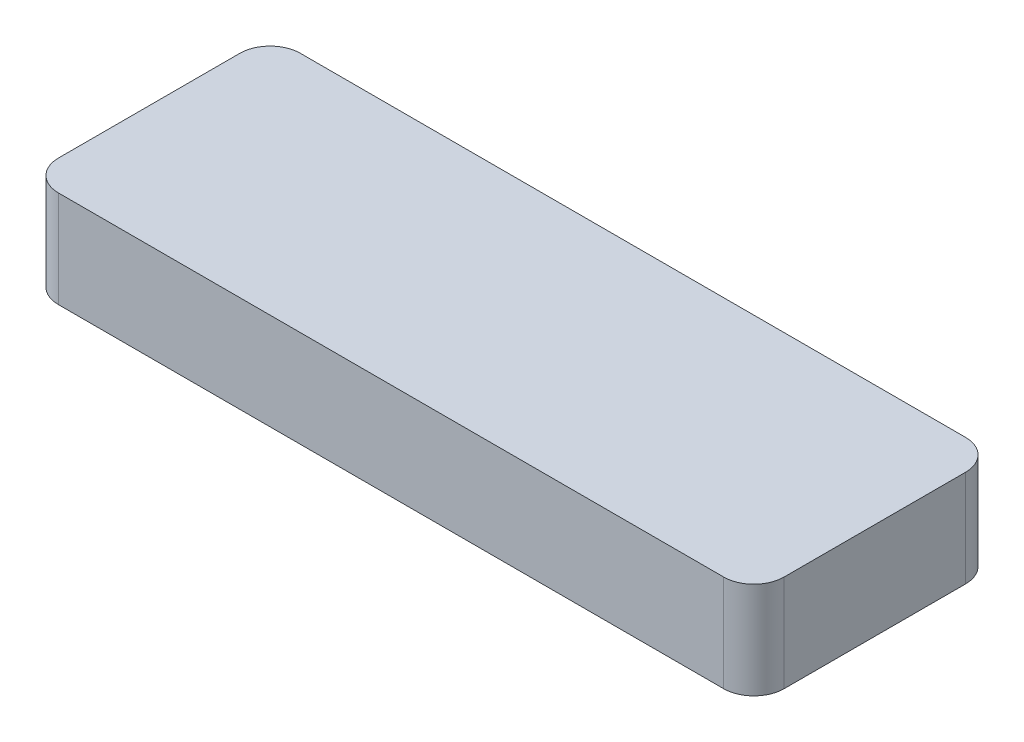
SolidWorks part; units mm, degrees
ref_plane "Alzado" through (0, 0, 0) normal (0, 0, 1) x (1, 0, 0)
ref_plane "Planta" through (0, 0, 0) normal (0, 1, 0) x (1, 0, 0)
ref_plane "Vista lateral" through (0, 0, 0) normal (1, 0, 0) x (0, 0, -1)
sketch "Croquis1" plane through (0, 0, 0) normal (0, 1, 0) x (1, 0, 0)
  line L1 (-60, 20) -> (60, 20)
  line L2 (-60, 20) -> (-60, -20)
  line L3 (-60, -20) -> (60, -20)
  line L4 (60, 20) -> (60, -20)
  line L5 (-60, 20) -> (60, -20) construction
  line L6 (-60, -20) -> (60, 20) construction
  point P0 (0, 0)
  dimension "D1" = 120
  dimension "D2" = 40
extrude "Saliente-Extruir1" add sketch "Croquis1" along normal blind 16
fillet "Redondeo1" radius 5 4 edges at (-60, 8, -20) (60, 8, -20) (60, 8, 20) (-60, 8, 20)
